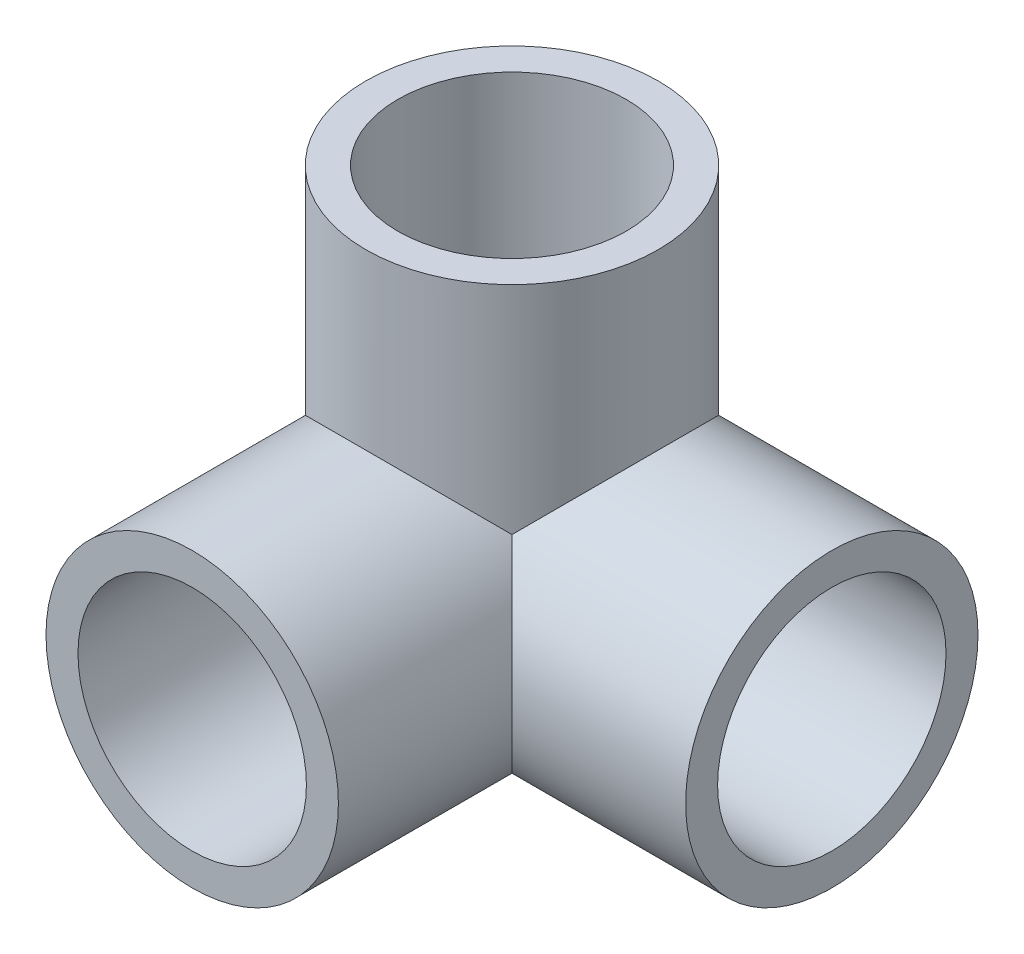
SolidWorks part; units mm, degrees
ref_plane "前视基准面" through (0, 0, 0) normal (0, 0, 1) x (1, 0, 0)
ref_plane "上视基准面" through (0, 0, 0) normal (0, 1, 0) x (1, 0, 0)
ref_plane "右视基准面" through (0, 0, 0) normal (1, 0, 0) x (0, 0, -1)
other "Configuration Table"
sketch "草图1" plane through (0, 0, 0) normal (0, 0, 1) x (1, 0, 0)
  circle A0 centre (0, 0) radius 12.5
  circle A1 centre (0, 0) radius 16
  dimension "D1" = 25
  dimension "D2" = 32
extrude "凸台-拉伸1" add sketch "草图1" along normal blind 35
sketch "草图2" plane through (0, 0, 0) normal (1, 0, 0) x (0, 0, -1)
  circle A0 centre (0, 0) radius 16
  circle A1 centre (0, 0) radius 12.5
  dimension "D1" = 32
  dimension "D2" = 25
extrude "凸台-拉伸2" add sketch "草图2" along normal blind 35
sketch "草图3" plane through (0, 0, 0) normal (0, 0, 1) x (1, 0, 0)
  line L0 (0, 16) -> (0, -16)
  arc A0 (0, 16) -> (0, -16) centre (0, 0) ccw
  circle A1 centre (0, 0) radius 16 construction
sketch "草图4" plane through (0, 0, 0) normal (0, 1, 0) x (1, 0, 0)
  circle A0 centre (0, 0) radius 16
  circle A1 centre (0, 0) radius 12.5
  dimension "D1" = 32
  dimension "D2" = 25
extrude "凸台-拉伸3" add sketch "草图4" along normal blind 35
revolve "旋转1" add sketch "草图3" angle 90 about L0
